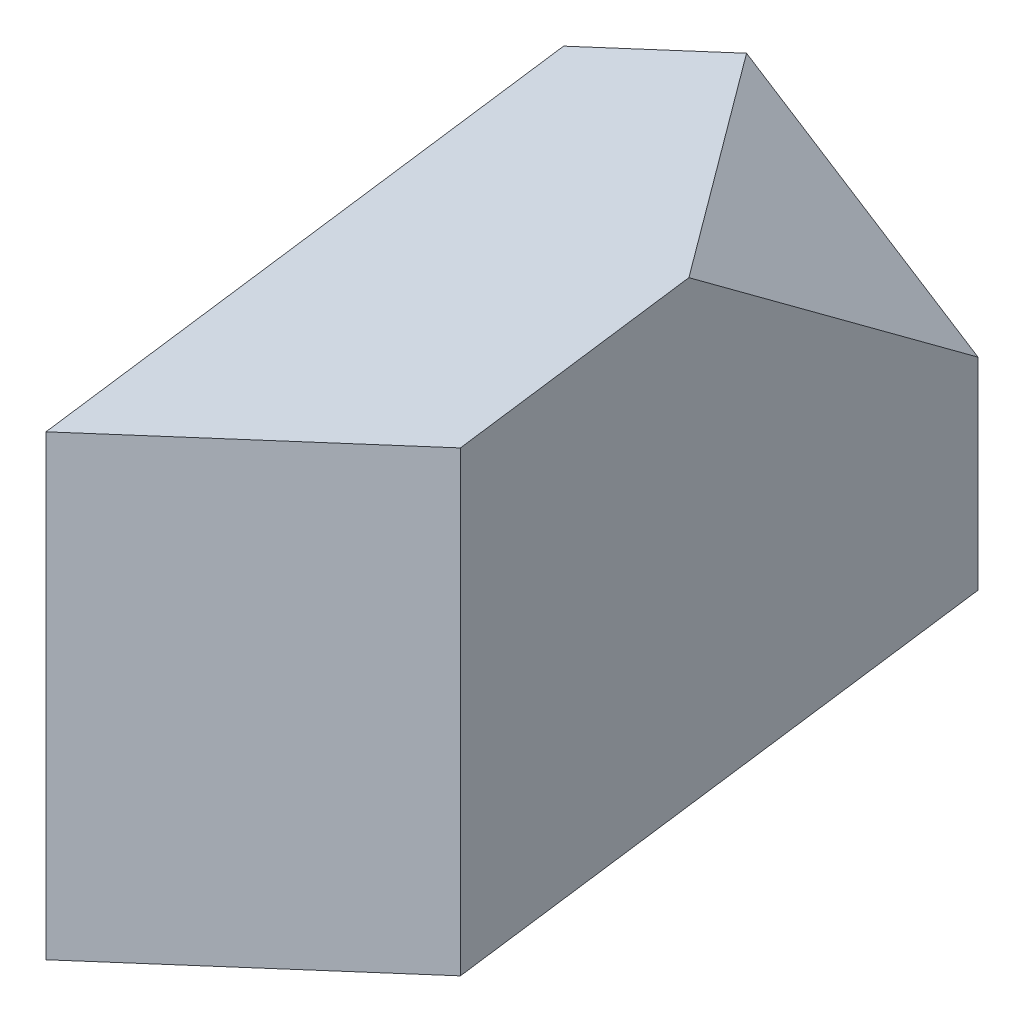
SolidWorks part; units mm, degrees
ref_plane "Ebene vorne" through (0, 0, 0) normal (0, 0, 1) x (1, 0, 0)
ref_plane "Ebene oben" through (0, 0, 0) normal (0, 1, 0) x (1, 0, 0)
ref_plane "Ebene rechts" through (0, 0, 0) normal (1, 0, 0) x (0, 0, -1)
sketch "SK Grundriss" plane through (0, 0, 0) normal (0, 0, 1) x (1, 0, 0)
  line L0 (0, 0) -> (54.3785, 25.3571)
  line L1 (0, 0) -> (0, 60)
  line L2 (54.3785, 25.3571) -> (54.3785, 85.3571)
  line L3 (0, 60) -> (54.3785, 85.3571)
  line L4 (54.3785, 85.3571) -> (0, 0) construction
  dimension "Winkel" = 65
  dimension "Seitenlänge" = 60
  dimension "Winkelhalbierende" = 32.5
sketch "SK Schnittebene" plane through (0, 0, 0) normal (1, 0, 0) x (0, 0, -1)
  line L0 (0, 0) -> (30, 0)
  dimension "Länge egal" = 30
ref_plane "E Schnittebene" through (0, 0, 0) normal (0.8434, -0.5373, 0) x (0, 0, -1)
sketch "SK Pfad" plane through (0, 0, 0) normal (0.8434, -0.5373, 0) x (0, 0, -1)
  line L0 (0, 0) -> (60, 0) construction
  line L1 (0, 0) -> (50.6035, 32.238)
  dimension "D1" = 60
  dimension "Länge" = 60
  dimension "Winkel" = 32.5
sweep "Austragung1" add profiles "SK Grundriss" path "SK Pfad"
ref_plane "Ebene1" through (48.0495, 75.4226, -32.456) normal (0.5051, 0.7928, -0.3412) x (0.8631, -0.4639, 0.1996)
ref_plane "Ebene2" through (58.6559, 92.0712, -39.6203) normal (0.5051, 0.7928, -0.3412) x (0.8631, -0.4639, 0.1996)
sketch "Skizze2" plane through (58.6559, 92.0712, -39.6203) normal (0.5051, 0.7928, -0.3412) x (0.8631, -0.4639, 0.1996)
  line L0 (15.1134, 15.2417) -> (-20.0764, 7.5936)
  line L1 (15.1134, 15.2417) -> (-20.0764, 7.5936)
  line L2 (3.9042, -17.9635) -> (-20.0764, 7.5936)
  line L3 (3.9042, -17.9635) -> (-20.0764, 7.5936)
  line L4 (15.1134, 15.2417) -> (3.9042, -17.9635)
  line L5 (15.1134, 15.2417) -> (3.9042, -17.9635)
extrude "Schnitt-Linear austragen1" cut sketch "Skizze2" along normal through all
